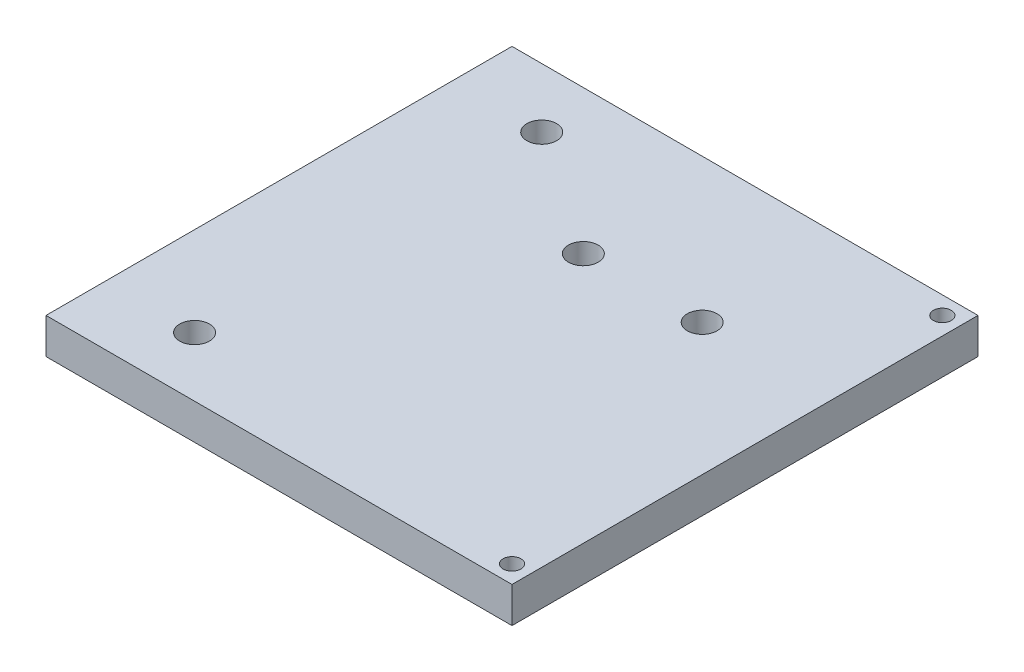
SolidWorks part; units mm, degrees
ref_plane "Front Plane" through (0, 0, 0) normal (0, 0, 1) x (1, 0, 0)
ref_plane "Top Plane" through (0, 0, 0) normal (0, 1, 0) x (1, 0, 0)
ref_plane "Right Plane" through (0, 0, 0) normal (1, 0, 0) x (0, 0, -1)
sketch "Sketch1" plane through (0, 0, 0) normal (0, 1, 0) x (1, 0, 0)
  line L0 (-39.2, 29.2) -> (-24.2, 29.2) construction
  line L1 (-39.2, -39.2) -> (39.2, -39.2)
  line L2 (-39.2, -39.2) -> (-39.2, 39.2)
  line L3 (-39.2, 39.2) -> (39.2, 39.2)
  line L4 (39.2, -39.2) -> (39.2, 39.2)
  line L5 (-39.2, -39.2) -> (39.2, 39.2) construction
  line L6 (-39.2, 39.2) -> (39.2, -39.2) construction
  line L7 (-39.2, -29.2) -> (-24.2, -29.2) construction
  circle A0 centre (-24.2, 29.2) radius 2.5
  circle A1 centre (-24.2, -29.2) radius 2.5
  circle A2 centre (36.2, 36.2) radius 1.5
  circle A3 centre (36.2, -36.2) radius 1.5
  circle A4 centre (-3, 15) radius 2.5
  circle A5 centre (17, 15) radius 2.5
  point P0 (0, 0)
  dimension "D3" = 5
  dimension "D7" = 3
  dimension "D11" = 5
  dimension "D1" = 78.4
  dimension "D2" = 78.4
  dimension "D4" = 15
  dimension "D5" = 10
  dimension "D6" = 10
  dimension "D8" = 3
  dimension "D9" = 3
  dimension "D10" = 20
  dimension "D12" = 15
  dimension "D13" = 3
extrude "Boss-Extrude1" add sketch "Sketch1" along normal blind 6
